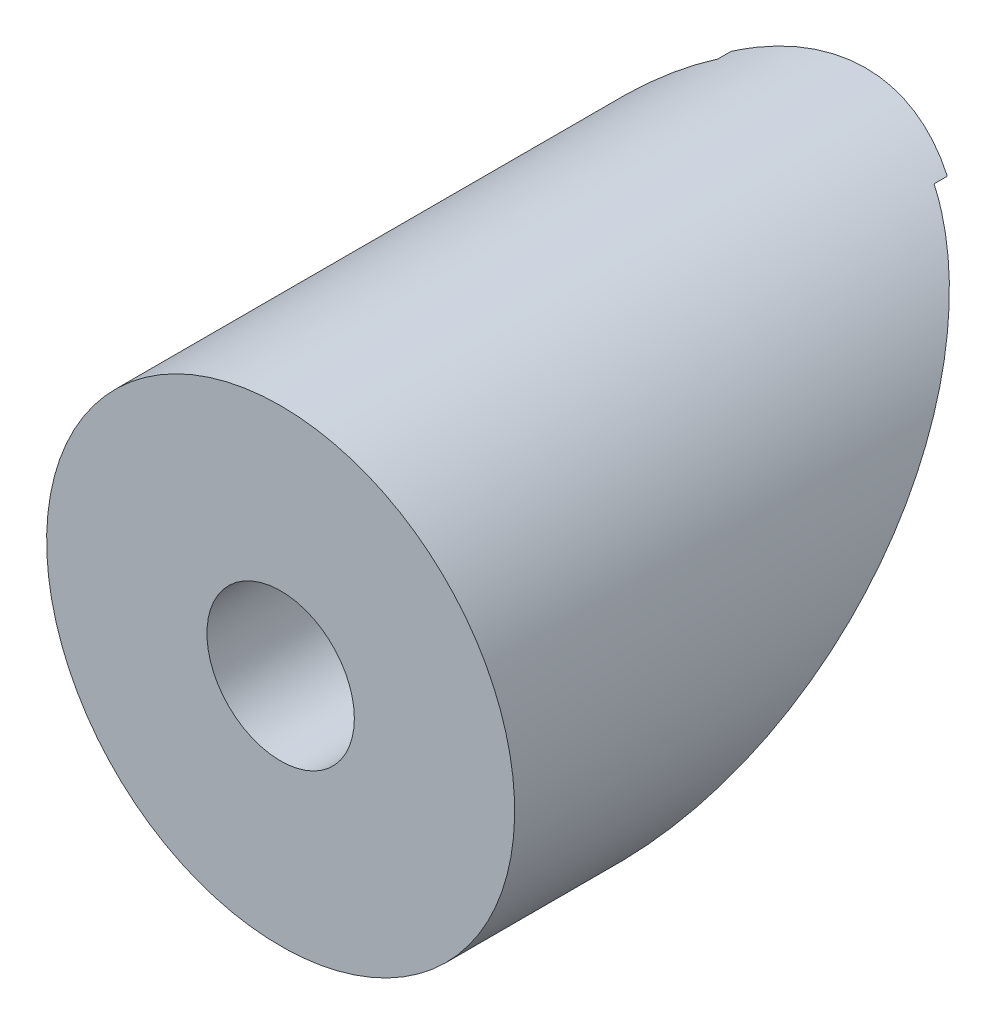
SolidWorks part; units mm, degrees
material "6061-T6 (SS)"
ref_plane "Front Plane" through (0, 0, 0) normal (0, 0, 1) x (1, 0, 0)
ref_plane "Top Plane" through (0, 0, 0) normal (0, 1, 0) x (1, 0, 0)
ref_plane "Right Plane" through (0, 0, 0) normal (1, 0, 0) x (0, 0, -1)
sketch "Sketch1" plane through (0, 0, 0) normal (1, 0, 0) x (0, 0, -1)
  line L0 (19.05, 9.525) -> (0, -9.525)
  line L1 (0, 9.525) -> (19.05, 9.525)
  line L2 (0, 9.525) -> (0, -9.525)
  point P1 (0, -9.525)
  dimension "D1" = 19.05
  dimension "D3" = 45
extrude "Boss-Extrude1" add sketch "Sketch1" along normal mid plane 19.05
sketch "Sketch2" plane through (0, -2.7898, 0) normal (0, 0, -1) x (1, 0, 0)
  circle A0 centre (0, -2.7898) radius 6.35
  point P2 (0, 0)
  point P4 (0, 0)
  point P5 (0, -3.8962)
  point P6 (0, 1.0461)
  point P7 (0, 1.6568)
  dimension "D1" = 12.7
extrude "Cut-Extrude1" cut sketch "Sketch2" against normal through all and the other way through all flip side to cut contours A0
sketch "Sketch3" plane through (0, 0, 0) normal (0, 0, 1) x (1, 0, 0)
  circle A0 centre (0, 0) radius 2
  point P2 (0, 0)
  point P4 (0, 0)
  point P5 (0, 0)
  point P11 (-6.3383, 0)
  point P13 (-6.3218, -0.6951)
  point P16 (-6.35, -0.2724)
  dimension "D1" = 4
extrude "Cut-Extrude2" cut sketch "Sketch3" against normal through all
sketch "Sketch11" plane through (0, 0, 0) normal (1, 0, 0) x (0, 0, -1)
  line L0 (15.1566, 5.6316) -> (14.7974, 5.6316)
  line L1 (3.175, -6.35) -> (15.875, 6.35) construction
  line L2 (14.7974, 5.6316) -> (3.8934, -5.2724)
  line L3 (3.8934, -5.2724) -> (3.8934, -5.6316)
  line L4 (3.8934, -5.6316) -> (15.1566, 5.6316)
  point P4 (15.875, 6.35)
  point P7 (3.175, -6.35)
  point P8 (0, 0)
  point P10 (0, 0)
  point P11 (0, 0)
  dimension "D1" = 0.254
  dimension "D2" = 1.016
  dimension "D3" = 1.016
extrude "Cut-Extrude6" cut sketch "Sketch11" against normal through all both and the other way through all
